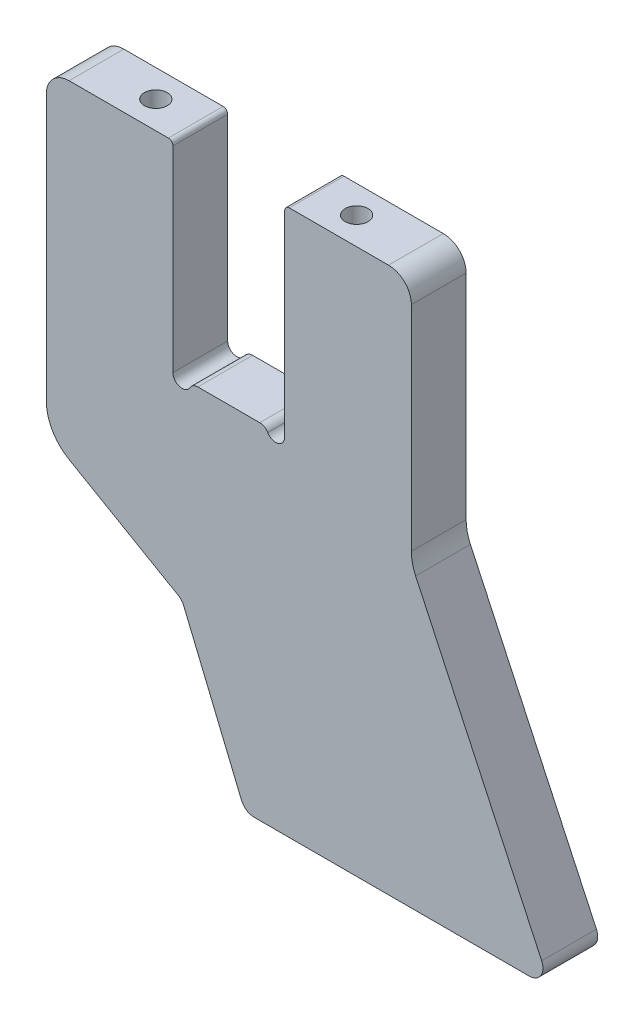
SolidWorks part; units mm, degrees
ref_plane "Plane1" through (0, 0, 0) normal (0, 0, 1) x (1, 0, 0)
ref_plane "Plane2" through (0, 0, 0) normal (0, 1, 0) x (1, 0, 0)
ref_plane "Plane3" through (0, 0, 0) normal (1, 0, 0) x (0, 0, -1)
sketch "Sketch1" plane through (0, 0, 0) normal (0, 0, 1) x (1, 0, 0)
  line L0 (-6.7859, 0) -> (6.7859, 0)
  line L1 (0, 0) -> (0, 32) construction
  line L2 (12.25, 0) -> (12.25, 43)
  line L3 (13.25, 44) -> (35, 44)
  line L4 (0, 0) -> (0, 42.7803) construction
  line L5 (-11.1451, -41.6594) -> (-35, -27.8868)
  line L6 (40.9369, -12.0092) -> (68.553, -71.2321)
  line L8 (65.8341, -75.5) -> (5.5477, -75.5)
  line L10 (2.776, -73.6481) -> (-9.8735, -43.1094)
  line L18 (40, -7.7831) -> (40, 39)
  line L23 (-40, -19.2265) -> (-40, 39)
  line L30 (-13.25, 44) -> (-35, 44)
  line L31 (-12.25, 0) -> (-12.25, 43)
  arc A0 (12.25, 0) -> (8.5179, -1) centre (10.25, 0) cw
  arc A1 (8.5179, -1) -> (6.7859, 0) centre (6.7859, -2) ccw
  arc A2 (-12.25, 0) -> (-8.5179, -1) centre (-10.25, 0) ccw
  arc A3 (-8.5179, -1) -> (-6.7859, 0) centre (-6.7859, -2) cw
  arc A4 (35, 44) -> (40, 39) centre (35, 39) cw
  arc A5 (-35, 44) -> (-40, 39) centre (-35, 39) ccw
  arc A7 (-13.25, 44) -> (-12.25, 43) centre (-13.25, 43) cw
  arc A11 (12.25, 43) -> (13.25, 44) centre (13.25, 43) cw
  arc A22 (-35, -27.8868) -> (-40, -19.2265) centre (-30, -19.2265) cw
  arc A23 (-9.8735, -43.1094) -> (-11.1451, -41.6594) centre (-12.6451, -44.2575) ccw
  arc A24 (40.9369, -12.0092) -> (40, -7.7831) centre (50, -7.7831) cw
  arc A25 (68.553, -71.2321) -> (65.8341, -75.5) centre (65.8341, -72.5) cw
  arc A26 (5.5477, -75.5) -> (2.776, -73.6481) centre (5.5477, -72.5) cw
  point P19 (-40, -25)
  point P53 (-12.25, 44)
  point P65 (12.25, 44)
  point P98 (40, -10)
  point P101 (70.5432, -75.5)
  point P104 (3.5432, -75.5)
  dimension "D13" = 5
  dimension "D23" = 2
  dimension "D21" = 10
  dimension "D29" = 3
  dimension "D30" = 10
  dimension "D31" = 3
  dimension "D11" = 1
  dimension "D4" = 25
  dimension "D5" = 40
  dimension "D6" = 119.5
  dimension "D7" = 24.5
  dimension "D8" = 22.5
  dimension "D9" = 54
  dimension "D10" = 69
  dimension "D12" = 44
  dimension "D16" = 67
  dimension "D17" = 80
  dimension "D28" = 60
extrude "Extrude1" add sketch "Sketch1" along normal blind 12
hole_wizard "2 stk M6" positions "Sketch3" profile "Sketch2" legacy
sketch "Sketch3" plane through (0, 44, 0) normal (0, 1, 0) x (-1, 0, 0)
  line L0 (0, 0) -> (0, 12) construction
  line L1 (-6.7859, 12) -> (6.7859, 12) construction
  line L3 (-22, 6) -> (0, 6) construction
  point P0 (-22, 6)
  point P13 (22, 6)
  dimension "D1" = 44
sketch "Sketch2" plane through (22, 44, 6) normal (1, 0, 0) x (0, 0, 1)
  line L0 (0, 0) -> (0, 15.5022)
  line L1 (0, 15.5022) -> (2.5, 14)
  line L2 (2.5, 14) -> (2.5, 0)
  line L4 (2.5, 0) -> (0, 0)
  line L6 (0, 15.5022) -> (-2.5, 14) construction
  line L7 (0, -4.2442) -> (0, 117.3081) construction
  dimension "Diameter" = 5
  dimension "Depth" = 14
  dimension "Drill Angle" = 118
cosmetic thread "Cosmetic Thread1" parameters "D1"=10, "D2"=6
cosmetic thread "Cosmetic Thread2" parameters "D1"=10, "D2"=6
